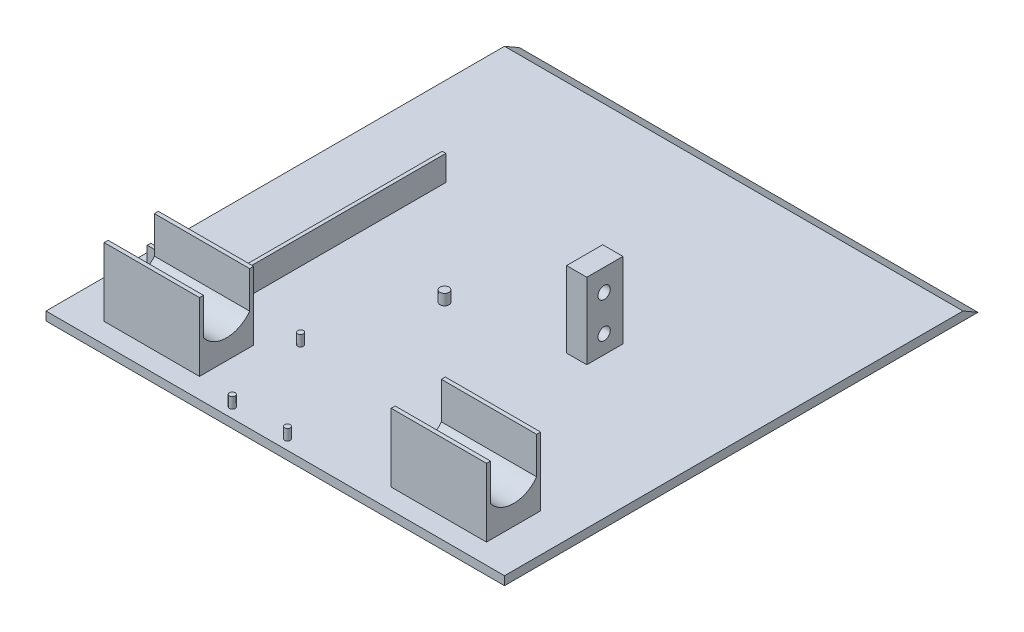
SolidWorks part; units mm, degrees
ref_plane "Front Plane" through (0, 0, 0) normal (0, 0, 1) x (1, 0, 0)
ref_plane "Top Plane" through (0, 0, 0) normal (0, 1, 0) x (1, 0, 0)
ref_plane "Right Plane" through (0, 0, 0) normal (1, 0, 0) x (0, 0, -1)
sketch "Sketch1" plane through (0, 0, 0) normal (0, 1, 0) x (1, 0, 0)
  line L1 (-63.5, -63.5) -> (63.5, -63.5)
  line L2 (-63.5, -63.5) -> (-63.5, 63.5)
  line L3 (-63.5, 63.5) -> (63.5, 63.5)
  line L4 (63.5, -63.5) -> (63.5, 63.5)
  line L5 (-63.5, -63.5) -> (63.5, 63.5) construction
  line L6 (-63.5, 63.5) -> (63.5, -63.5) construction
  point P0 (0, 0)
  dimension "D1" = 127
  dimension "D2" = 127
extrude "Boss-Extrude1" add sketch "Sketch1" along normal blind 2.4
sketch "Sketch2" plane through (0, 2.4, 0) normal (0, 1, 0) x (1, 0, 0)
  line L0 (-52.948, -42.9348) -> (-26.548, -42.9348)
  line L1 (-26.548, -42.9348) -> (-26.548, -57.9348)
  line L2 (-52.948, -42.9348) -> (-52.948, -57.9348)
  line L3 (-52.948, -57.9348) -> (-26.548, -57.9348)
  line L5 (-53.548, -44.5348) -> (-26.548, -44.5348) construction
  line L6 (-53.548, -56.3348) -> (-26.548, -56.3348) construction
  line L7 (-53.048, -57.9348) -> (-53.048, -56.3348) construction
  dimension "D1" = 1.6
  dimension "D2" = 1.6
  dimension "D3" = 0.1
extrude "Boss-Extrude3" add sketch "Sketch2" along normal blind 5.5
sketch "Sketch3" plane through (0, 7.9, 0) normal (0, 1, 0) x (1, 0, 0)
  line L0 (-52.948, -44.0348) -> (-26.548, -44.0348)
  line L1 (-52.948, -42.9348) -> (-52.948, -57.9348) construction
  line L2 (-26.548, -57.9348) -> (-26.548, -42.9348) construction
  line L3 (-26.548, -44.0348) -> (-26.548, -56.8348)
  line L4 (-26.548, -56.8348) -> (-52.948, -56.8348)
  line L5 (-52.948, -56.8348) -> (-52.948, -44.0348)
  line L6 (-53.548, -44.5348) -> (-26.548, -44.5348) construction
  line L7 (-53.548, -56.3348) -> (-26.548, -56.3348) construction
  dimension "D1" = 0.5
  dimension "D2" = 0.5
extrude "Boss-Extrude4" add sketch "Sketch3" along normal up to surface (3.2061 mm away)
sketch "Sketch4" plane through (0, 7.9, 0) normal (0, 1, 0) x (1, 0, 0)
  line L0 (-52.948, -42.9348) -> (-52.948, -44.0348)
  line L1 (-52.948, -44.0348) -> (-26.548, -44.0348)
  line L2 (-52.948, -44.0348) -> (-26.548, -44.0348) construction
  line L3 (-26.548, -44.0348) -> (-26.548, -42.9348)
  line L4 (-26.548, -42.9348) -> (-52.948, -42.9348)
  line L5 (-52.948, -56.8348) -> (-52.948, -57.9348)
  line L6 (-52.948, -56.8348) -> (-52.948, -57.9348) construction
  line L7 (-52.948, -57.9348) -> (-26.548, -57.9348) construction
  line L8 (-52.948, -57.9348) -> (-26.548, -57.9348)
  line L9 (-26.548, -57.9348) -> (-26.548, -56.8348)
  line L10 (-52.948, -56.8348) -> (-26.548, -56.8348) construction
  line L11 (-26.548, -57.9348) -> (-26.548, -56.8348) construction
  line L12 (-26.548, -56.8348) -> (-52.948, -56.8348)
extrude "Boss-Extrude5" add sketch "Sketch4" along normal up to vertex (3.2061 mm away)
mirror "Mirror1" about plane through (0, 0, 0) normal (1, 0, 0) of "Boss-Extrude3"
mirror "Mirror2" about plane through (0, 0, 0) normal (1, 0, 0) of "Boss-Extrude5"
mirror "Mirror3" about plane through (0, 0, 0) normal (1, 0, 0) of "Boss-Extrude4"
sketch "Sketch6" plane through (0, 2.4, 0) normal (0, 1, 0) x (1, 0, 0)
  line L0 (-58.2564, -39.7188) -> (-58.2564, -40.7188)
  line L1 (-58.2564, -40.7188) -> (-38.9437, -40.7188)
  line L2 (-38.9437, -40.7188) -> (-38.9437, 22.696)
  line L3 (-38.9437, 22.696) -> (-39.9437, 22.696)
  line L6 (-39.9437, 22.696) -> (-39.9437, -39.7188)
  line L7 (-39.9437, -39.7188) -> (-58.2564, -39.7188)
  dimension "D1" = 1
  dimension "D2" = 1
extrude "Boss-Extrude8" add sketch "Sketch6" along normal blind 7
sketch "Sketch7" plane through (0, 2.4, 0) normal (0, 1, 0) x (1, 0, 0)
  circle A0 centre (-20.1578, -36.324) radius 0.8
  circle A1 centre (-35.4578, -36.324) radius 0.8
  circle A2 centre (-14.7007, -60.6984) radius 0.8
  circle A3 centre (0.5993, -60.6984) radius 0.8
  dimension "D1" = 1.6
  dimension "D2" = 1.6
  dimension "D3" = 1.6
  dimension "D4" = 1.6
extrude "Boss-Extrude9" add sketch "Sketch7" along normal blind 3
sketch "Sketch8" plane through (0, 2.4, 0) normal (0, 1, 0) x (1, 0, 0)
  circle A0 centre (-10.4111, -6.1968) radius 1.25
  dimension "D1" = 2.5
extrude "Boss-Extrude10" add sketch "Sketch8" along normal blind 3
sketch "Sketch9" plane through (0, 2.4, 0) normal (0, 1, 0) x (1, 0, 0)
  line L0 (18.7, -1.5) -> (24.3, -1.5)
  line L1 (44.1, -1.5) -> (10.5, -1.5) construction
  line L2 (24.3, -1.5) -> (24.3, 8.5)
  line L3 (24.3, 8.5) -> (18.7, 8.5)
  line L4 (18.7, 8.5) -> (18.7, -1.5)
  dimension "D1" = 10
extrude "Boss-Extrude11" add sketch "Sketch9" along normal blind 21
sketch "Sketch10" plane through (24.3, 0, 0) normal (1, 0, 0) x (0, 0, -1)
  circle A0 centre (3.3, 17.35) radius 1.7
  circle A1 centre (3.3, 7.45) radius 1.7
  dimension "D1" = 3.4
  dimension "D2" = 3.4
extrude "Cut-Extrude1" cut sketch "Sketch10" against normal up to surface (5.6 mm away) up to face at (18.7, 12.9, -3.5)
sketch "Sketch11" plane through (63.5, 0, 0) normal (1, 0, 0) x (0, 0, -1)
  line L0 (63.5, 2.4) -> (67.6569, 0)
  line L1 (67.6569, 0) -> (63.5, 0)
  line L2 (63.5, 2.4) -> (19.5059, 27.8) construction
  line L3 (63.5, 2.4) -> (63.5, 0)
extrude "Boss-Extrude12" add sketch "Sketch11" against normal up to surface (127 mm away) up to face at (-63.5, 1.2, 0)
